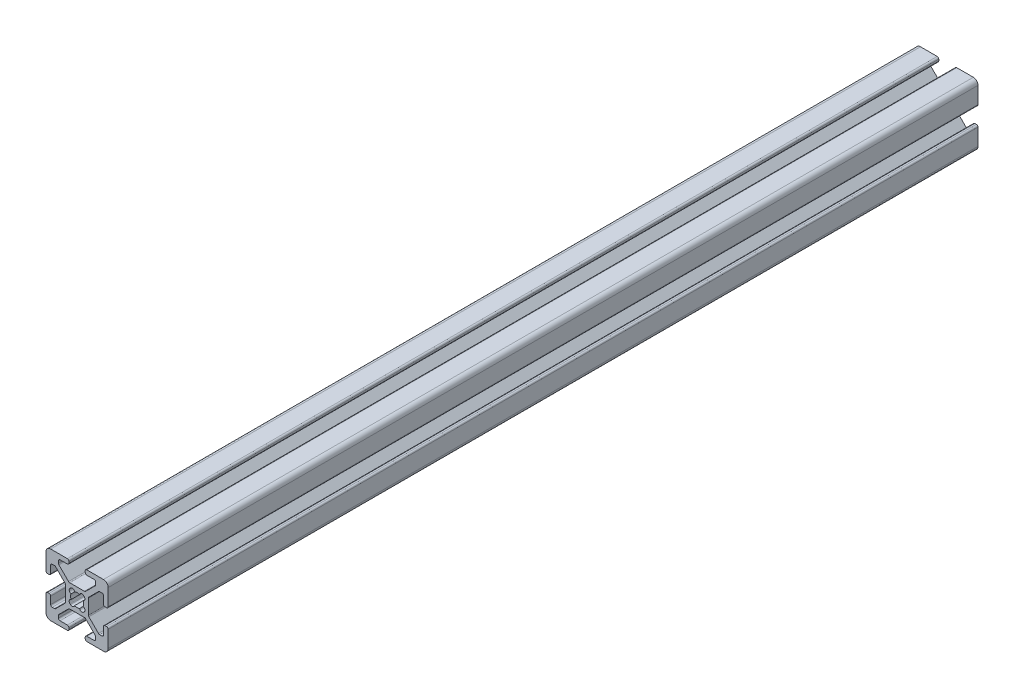
SolidWorks part; units mm, degrees
material "6061 Alloy"
ref_plane "Front Plane" through (0, 0, 0) normal (0, 0, 1) x (1, 0, 0)
ref_plane "Top Plane" through (0, 0, 0) normal (0, 1, 0) x (1, 0, 0)
ref_plane "Right Plane" through (0, 0, 0) normal (1, 0, 0) x (0, 0, -1)
ref_plane "Plane1" through (0, 0, 4000) normal (0, 0, 1) x (1, 0, 0)
sketch "Sketch1" plane through (0, 0, 4000) normal (0, 0, 1) x (1, 0, 0)
  line B0 (10, 3.138) -> (10, 8.5)
  line B1 (8.5, 10) -> (3.138, 10)
  line B2 (2.63, 9.492) -> (2.63, 9.008)
  line B3 (3.138, 8.5) -> (5.487, 8.5)
  line B4 (5.995, 7.992) -> (5.995, 7.2661)
  line B5 (5.8462, 6.9069) -> (2.7431, 3.8038)
  line B6 (2.3839, 3.655) -> (-2.3839, 3.655)
  line B7 (-2.7431, 3.8038) -> (-5.8462, 6.9069)
  line B8 (-5.995, 7.2661) -> (-5.995, 7.992)
  line B9 (-5.487, 8.5) -> (-3.138, 8.5)
  line B10 (-2.63, 9.008) -> (-2.63, 9.492)
  line B11 (-3.138, 10) -> (-8.5, 10)
  line B12 (-10, 8.5) -> (-10, 3.138)
  line B13 (-9.492, 2.63) -> (-9.008, 2.63)
  line B14 (-8.5, 3.138) -> (-8.5, 5.487)
  line B15 (-7.992, 5.995) -> (-7.2661, 5.995)
  line B16 (-6.9069, 5.8462) -> (-3.8038, 2.7431)
  line B17 (-3.655, 2.3839) -> (-3.655, -2.3839)
  line B18 (-3.8038, -2.7431) -> (-6.9069, -5.8462)
  line B19 (-7.2661, -5.995) -> (-7.992, -5.995)
  line B20 (-8.5, -5.487) -> (-8.5, -3.138)
  line B21 (-9.008, -2.63) -> (-9.492, -2.63)
  line B22 (-10, -3.138) -> (-10, -8.5)
  line B23 (-8.5, -10) -> (-3.138, -10)
  line B24 (-2.63, -9.492) -> (-2.63, -9.008)
  line B25 (-3.138, -8.5) -> (-5.487, -8.5)
  line B26 (-5.995, -7.992) -> (-5.995, -7.2661)
  line B27 (-5.8462, -6.9069) -> (-2.7431, -3.8038)
  line B28 (-2.3839, -3.655) -> (2.3839, -3.655)
  line B29 (2.7431, -3.8038) -> (5.8462, -6.9069)
  line B30 (5.995, -7.2661) -> (5.995, -7.992)
  line B31 (5.487, -8.5) -> (3.138, -8.5)
  line B32 (2.63, -9.008) -> (2.63, -9.492)
  line B33 (3.138, -10) -> (8.5, -10)
  line B34 (10, -8.5) -> (10, -3.138)
  line B35 (9.492, -2.63) -> (9.008, -2.63)
  line B36 (8.5, -3.138) -> (8.5, -5.487)
  line B37 (7.992, -5.995) -> (7.2661, -5.995)
  line B38 (6.9069, -5.8462) -> (3.8038, -2.7431)
  line B39 (3.655, -2.3839) -> (3.655, 2.3839)
  line B40 (3.8038, 2.7431) -> (6.9069, 5.8462)
  line B41 (7.2661, 5.995) -> (7.992, 5.995)
  line B42 (8.5, 5.487) -> (8.5, 3.138)
  line B43 (9.008, 2.63) -> (9.492, 2.63)
  line B44 (-2.1249, -2.3045) -> (-2.3045, -2.1249)
  line B45 (-2.3045, 2.1249) -> (-2.1249, 2.3045)
  line B46 (2.1249, 2.3045) -> (2.3045, 2.1249)
  line B47 (2.3045, -2.1249) -> (2.1249, -2.3045)
  arc B48 (9.492, 2.63) -> (10, 3.138) centre (9.492, 3.138) ccw
  arc B49 (10, 8.5) -> (8.5, 10) centre (8.5, 8.5) ccw
  arc B50 (3.138, 10) -> (2.63, 9.492) centre (3.138, 9.492) ccw
  arc B51 (2.63, 9.008) -> (3.138, 8.5) centre (3.138, 9.008) ccw
  arc B52 (5.487, 8.5) -> (5.995, 7.992) centre (5.487, 7.992) cw
  arc B53 (5.995, 7.2661) -> (5.8462, 6.9069) centre (5.487, 7.2661) cw
  arc B54 (2.7431, 3.8038) -> (2.3839, 3.655) centre (2.3839, 4.163) cw
  arc B55 (-2.3839, 3.655) -> (-2.7431, 3.8038) centre (-2.3839, 4.163) cw
  arc B56 (-5.8462, 6.9069) -> (-5.995, 7.2661) centre (-5.487, 7.2661) cw
  arc B57 (-5.995, 7.992) -> (-5.487, 8.5) centre (-5.487, 7.992) cw
  arc B58 (-3.138, 8.5) -> (-2.63, 9.008) centre (-3.138, 9.008) ccw
  arc B59 (-2.63, 9.492) -> (-3.138, 10) centre (-3.138, 9.492) ccw
  arc B60 (-8.5, 10) -> (-10, 8.5) centre (-8.5, 8.5) ccw
  arc B61 (-10, 3.138) -> (-9.492, 2.63) centre (-9.492, 3.138) ccw
  arc B62 (-9.008, 2.63) -> (-8.5, 3.138) centre (-9.008, 3.138) ccw
  arc B63 (-8.5, 5.487) -> (-7.992, 5.995) centre (-7.992, 5.487) cw
  arc B64 (-7.2661, 5.995) -> (-6.9069, 5.8462) centre (-7.2661, 5.487) cw
  arc B65 (-3.8038, 2.7431) -> (-3.655, 2.3839) centre (-4.163, 2.3839) cw
  arc B66 (-3.655, -2.3839) -> (-3.8038, -2.7431) centre (-4.163, -2.3839) cw
  arc B67 (-6.9069, -5.8462) -> (-7.2661, -5.995) centre (-7.2661, -5.487) cw
  arc B68 (-7.992, -5.995) -> (-8.5, -5.487) centre (-7.992, -5.487) cw
  arc B69 (-8.5, -3.138) -> (-9.008, -2.63) centre (-9.008, -3.138) ccw
  arc B70 (-9.492, -2.63) -> (-10, -3.138) centre (-9.492, -3.138) ccw
  arc B71 (-10, -8.5) -> (-8.5, -10) centre (-8.5, -8.5) ccw
  arc B72 (-3.138, -10) -> (-2.63, -9.492) centre (-3.138, -9.492) ccw
  arc B73 (-2.63, -9.008) -> (-3.138, -8.5) centre (-3.138, -9.008) ccw
  arc B74 (-5.487, -8.5) -> (-5.995, -7.992) centre (-5.487, -7.992) cw
  arc B75 (-5.995, -7.2661) -> (-5.8462, -6.9069) centre (-5.487, -7.2661) cw
  arc B76 (-2.7431, -3.8038) -> (-2.3839, -3.655) centre (-2.3839, -4.163) cw
  arc B77 (2.3839, -3.655) -> (2.7431, -3.8038) centre (2.3839, -4.163) cw
  arc B78 (5.8462, -6.9069) -> (5.995, -7.2661) centre (5.487, -7.2661) cw
  arc B79 (5.995, -7.992) -> (5.487, -8.5) centre (5.487, -7.992) cw
  arc B80 (3.138, -8.5) -> (2.63, -9.008) centre (3.138, -9.008) ccw
  arc B81 (2.63, -9.492) -> (3.138, -10) centre (3.138, -9.492) ccw
  arc B82 (8.5, -10) -> (10, -8.5) centre (8.5, -8.5) ccw
  arc B83 (10, -3.138) -> (9.492, -2.63) centre (9.492, -3.138) ccw
  arc B84 (9.008, -2.63) -> (8.5, -3.138) centre (9.008, -3.138) ccw
  arc B85 (8.5, -5.487) -> (7.992, -5.995) centre (7.992, -5.487) cw
  arc B86 (7.2661, -5.995) -> (6.9069, -5.8462) centre (7.2661, -5.487) cw
  arc B87 (3.8038, -2.7431) -> (3.655, -2.3839) centre (4.163, -2.3839) cw
  arc B88 (3.655, 2.3839) -> (3.8038, 2.7431) centre (4.163, 2.3839) cw
  arc B89 (6.9069, 5.8462) -> (7.2661, 5.995) centre (7.2661, 5.487) cw
  arc B90 (7.992, 5.995) -> (8.5, 5.487) centre (7.992, 5.487) cw
  arc B91 (8.5, 3.138) -> (9.008, 2.63) centre (9.008, 3.138) ccw
  arc B92 (0.804, -1.9351) -> (-0.804, -1.9351) centre (0, 0) cw
  arc B93 (-0.804, -1.9351) -> (-2.1249, -2.3045) centre (-1.5684, -1.748) cw
  arc B94 (-2.3045, -2.1249) -> (-1.9351, -0.804) centre (-1.748, -1.5684) cw
  arc B95 (-1.9351, -0.804) -> (-1.9351, 0.804) centre (0, 0) cw
  arc B96 (-1.9351, 0.804) -> (-2.3045, 2.1249) centre (-1.748, 1.5684) cw
  arc B97 (-2.1249, 2.3045) -> (-0.804, 1.9351) centre (-1.5684, 1.748) cw
  arc B98 (-0.804, 1.9351) -> (0.804, 1.9351) centre (0, 0) cw
  arc B99 (0.804, 1.9351) -> (2.1249, 2.3045) centre (1.5684, 1.748) cw
  arc B100 (2.3045, 2.1249) -> (1.9351, 0.804) centre (1.748, 1.5684) cw
  arc B101 (1.9351, 0.804) -> (1.9351, -0.804) centre (0, 0) cw
  arc B102 (1.9351, -0.804) -> (2.3045, -2.1249) centre (1.748, -1.5684) cw
  arc B103 (2.1249, -2.3045) -> (0.804, -1.9351) centre (1.5684, -1.748) cw
sketch_block_instance "Block1-1"
sketch_block "Block1"
extrude "Boss-Extrude1" add sketch "Sketch1" against normal blind 280
